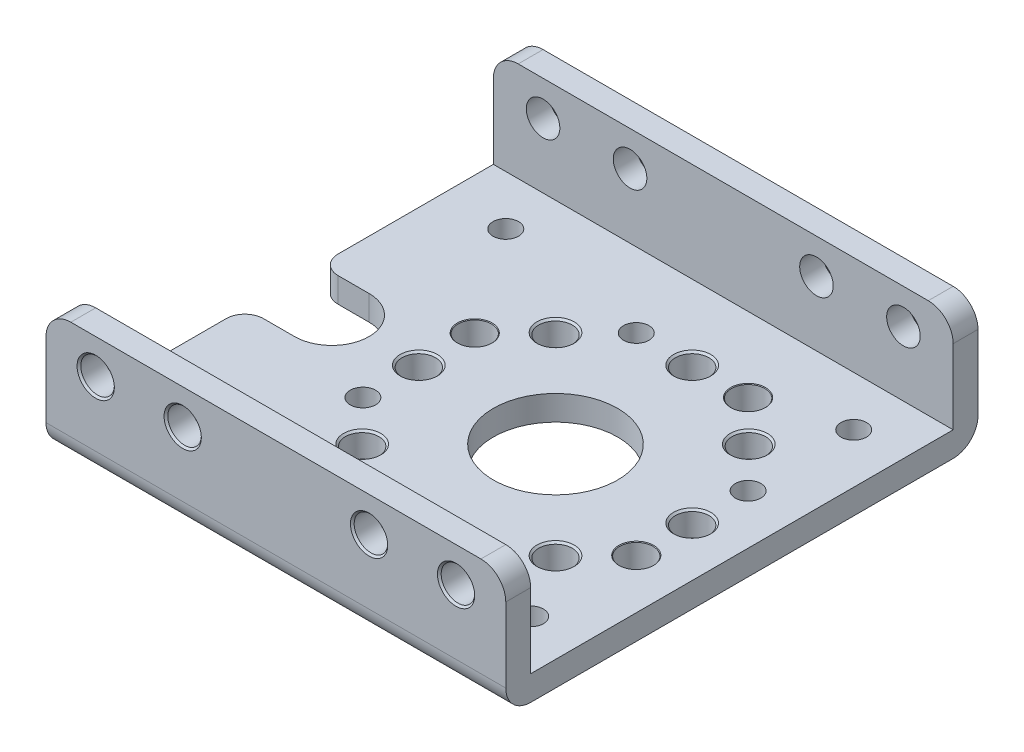
SolidWorks part; units mm, degrees
ref_plane "Front Plane" through (0, 0, 0) normal (0, 0, 1) x (1, 0, 0)
ref_plane "Top Plane" through (0, 0, 0) normal (0, 1, 0) x (1, 0, 0)
ref_plane "Right Plane" through (0, 0, 0) normal (1, 0, 0) x (0, 0, -1)
ref_plane "Plane1" through (0, 10, 0) normal (0, 1, 0) x (-1, 0, 0)
sketch "Sketch1" plane through (0, 10, 0) normal (0, 1, 0) x (-1, 0, 0)
  line L0 (22, 19) -> (-15, 19)
  line L1 (-15, 19) -> (-15, -19)
  line L2 (-15, -19) -> (22, -19)
  line L3 (22, -19) -> (22, 19)
extrude "Boss-Extrude1" add sketch "Sketch1" against normal blind 10
sketch "Sketch2" plane through (15, 0, 0) normal (1, 0, 0) x (0, 0, -1)
  line L0 (17, 10) -> (-17, 10)
  line L1 (-17, 10) -> (-17, 2)
  line L2 (-17, 2) -> (17, 2)
  line L3 (17, 2) -> (17, 10)
extrude "Cut-Extrude1" cut sketch "Sketch2" against normal through all
sketch "Sketch3" plane through (0, 2, 0) normal (0, 1, 0) x (-1, 0, 0)
  line L0 (22, -3) -> (22, 3)
  line L1 (22, 3) -> (18, 3)
  line L2 (18, -3) -> (22, -3)
  arc A0 (18, 3) -> (18, -3) centre (18, 0) ccw
extrude "Cut-Extrude2" cut sketch "Sketch3" against normal through all
hole_wizard "Hole1" positions "Sketch5" profile "Sketch4" legacy
sketch "Sketch5" plane through (0, 0, 0) normal (0, -1, 0) x (1, 0, 0)
  point P0 (-4.5, -11)
sketch "Sketch4" plane through (-4.5, 0, -11) normal (1, 0, 0) x (0, 0, -1)
  line L0 (0, 0) -> (0, 10)
  line L1 (0, 10) -> (1.025, 10)
  line L2 (1.025, 10) -> (1.025, 0)
  line L3 (1.025, 0) -> (0, 0)
  line L4 (0, 110) -> (0, -10) construction
  dimension "Diameter" = 2.05
  dimension "Depth" = 10
hole_wizard "Hole2" positions "Sketch7" profile "Sketch6" legacy
sketch "Sketch7" plane through (0, 0, 0) normal (0, -1, 0) x (1, 0, 0)
  point P0 (-11, 4.5)
sketch "Sketch6" plane through (-11, 0, 4.5) normal (1, 0, 0) x (0, 0, -1)
  line L0 (0, 0) -> (0, 10)
  line L1 (0, 10) -> (1.025, 10)
  line L2 (1.025, 10) -> (1.025, 0)
  line L3 (1.025, 0) -> (0, 0)
  line L4 (0, 110) -> (0, -10) construction
  dimension "Diameter" = 2.05
  dimension "Depth" = 10
hole_wizard "Hole3" positions "Sketch9" profile "Sketch8" legacy
sketch "Sketch9" plane through (0, 0, 0) normal (0, -1, 0) x (1, 0, 0)
  point P0 (4.5, 11)
sketch "Sketch8" plane through (4.5, 0, 11) normal (1, 0, 0) x (0, 0, -1)
  line L0 (0, 0) -> (0, 10)
  line L1 (0, 10) -> (1.025, 10)
  line L2 (1.025, 10) -> (1.025, 0)
  line L3 (1.025, 0) -> (0, 0)
  line L4 (0, 110) -> (0, -10) construction
  dimension "Diameter" = 2.05
  dimension "Depth" = 10
hole_wizard "Hole4" positions "Sketch11" profile "Sketch10" legacy
sketch "Sketch11" plane through (0, 0, 0) normal (0, -1, 0) x (1, 0, 0)
  point P0 (11, -4.5)
sketch "Sketch10" plane through (11, 0, -4.5) normal (1, 0, 0) x (0, 0, -1)
  line L0 (0, 0) -> (0, 10)
  line L1 (0, 10) -> (1.025, 10)
  line L2 (1.025, 10) -> (1.025, 0)
  line L3 (1.025, 0) -> (0, 0)
  line L4 (0, 110) -> (0, -10) construction
  dimension "Diameter" = 2.05
  dimension "Depth" = 10
hole_wizard "Hole5" positions "Sketch13" profile "Sketch12" legacy
sketch "Sketch13" plane through (0, 0, 0) normal (0, -1, 0) x (1, 0, 0)
  point P0 (-17, 13)
sketch "Sketch12" plane through (-17, 0, 13) normal (1, 0, 0) x (0, 0, -1)
  line L0 (0, 0) -> (0, 10)
  line L1 (0, 10) -> (1.025, 10)
  line L2 (1.025, 10) -> (1.025, 0)
  line L3 (1.025, 0) -> (0, 0)
  line L4 (0, 110) -> (0, -10) construction
  dimension "Diameter" = 2.05
  dimension "Depth" = 10
hole_wizard "Hole6" positions "Sketch15" profile "Sketch14" legacy
sketch "Sketch15" plane through (0, 0, 0) normal (0, -1, 0) x (1, 0, 0)
  point P0 (-17, -13)
sketch "Sketch14" plane through (-17, 0, -13) normal (1, 0, 0) x (0, 0, -1)
  line L0 (0, 0) -> (0, 10)
  line L1 (0, 10) -> (1.025, 10)
  line L2 (1.025, 10) -> (1.025, 0)
  line L3 (1.025, 0) -> (0, 0)
  line L4 (0, 110) -> (0, -10) construction
  dimension "Diameter" = 2.05
  dimension "Depth" = 10
hole_wizard "Hole7" positions "Sketch17" profile "Sketch16" legacy
sketch "Sketch17" plane through (0, 0, 0) normal (0, -1, 0) x (1, 0, 0)
  point P0 (11, 13)
sketch "Sketch16" plane through (11, 0, 13) normal (1, 0, 0) x (0, 0, -1)
  line L0 (0, 0) -> (0, 10)
  line L1 (0, 10) -> (1.025, 10)
  line L2 (1.025, 10) -> (1.025, 0)
  line L3 (1.025, 0) -> (0, 0)
  line L4 (0, 110) -> (0, -10) construction
  dimension "Diameter" = 2.05
  dimension "Depth" = 10
hole_wizard "Hole8" positions "Sketch19" profile "Sketch18" legacy
sketch "Sketch19" plane through (0, 0, 0) normal (0, -1, 0) x (1, 0, 0)
  point P0 (11, -13)
sketch "Sketch18" plane through (11, 0, -13) normal (1, 0, 0) x (0, 0, -1)
  line L0 (0, 0) -> (0, 10)
  line L1 (0, 10) -> (1.025, 10)
  line L2 (1.025, 10) -> (1.025, 0)
  line L3 (1.025, 0) -> (0, 0)
  line L4 (0, 110) -> (0, -10) construction
  dimension "Diameter" = 2.05
  dimension "Depth" = 10
hole_wizard "Hole9" positions "Sketch21" profile "Sketch20" legacy
sketch "Sketch21" plane through (0, 0, 0) normal (0, -1, 0) x (1, 0, 0)
  point P0 (0, 0)
sketch "Sketch20" plane through (0, 0, 0) normal (1, 0, 0) x (0, 0, -1)
  line L0 (0, 0) -> (0, 10)
  line L1 (0, 10) -> (5, 10)
  line L2 (5, 10) -> (5, 0)
  line L3 (5, 0) -> (0, 0)
  line L4 (0, 110) -> (0, -10) construction
  dimension "Diameter" = 10
  dimension "Depth" = 10
hole_wizard "Hole10" positions "Sketch23" profile "Sketch22" legacy
sketch "Sketch23" plane through (0, 2, 0) normal (0, 1, 0) x (-1, 0, 0)
  point P0 (11, -4.5)
sketch "Sketch22" plane through (-11, 2, -4.5) normal (1, 0, 0) x (0, 0, 1)
  line L0 (0, 0) -> (0, 2)
  line L1 (0, 2) -> (1.35, 2)
  line L2 (1.35, 2) -> (1.35, 0)
  line L3 (1.35, 0) -> (0, 0)
  line L4 (0, 110) -> (0, -10) construction
  dimension "Diameter" = 2.7
  dimension "Depth" = 2
hole_wizard "Hole11" positions "Sketch25" profile "Sketch24" legacy
sketch "Sketch25" plane through (0, 2, 0) normal (0, 1, 0) x (-1, 0, 0)
  point P0 (4.5, 11)
sketch "Sketch24" plane through (-4.5, 2, 11) normal (1, 0, 0) x (0, 0, 1)
  line L0 (0, 0) -> (0, 2)
  line L1 (0, 2) -> (1.35, 2)
  line L2 (1.35, 2) -> (1.35, 0)
  line L3 (1.35, 0) -> (0, 0)
  line L4 (0, 110) -> (0, -10) construction
  dimension "Diameter" = 2.7
  dimension "Depth" = 2
hole_wizard "Hole12" positions "Sketch27" profile "Sketch26" legacy
sketch "Sketch27" plane through (0, 2, 0) normal (0, 1, 0) x (-1, 0, 0)
  point P0 (-11, 4.5)
sketch "Sketch26" plane through (11, 2, 4.5) normal (1, 0, 0) x (0, 0, 1)
  line L0 (0, 0) -> (0, 2)
  line L1 (0, 2) -> (1.35, 2)
  line L2 (1.35, 2) -> (1.35, 0)
  line L3 (1.35, 0) -> (0, 0)
  line L4 (0, 110) -> (0, -10) construction
  dimension "Diameter" = 2.7
  dimension "Depth" = 2
hole_wizard "Hole13" positions "Sketch29" profile "Sketch28" legacy
sketch "Sketch29" plane through (0, 2, 0) normal (0, 1, 0) x (-1, 0, 0)
  point P0 (-4.5, -11)
sketch "Sketch28" plane through (4.5, 2, -11) normal (1, 0, 0) x (0, 0, 1)
  line L0 (0, 0) -> (0, 2)
  line L1 (0, 2) -> (1.35, 2)
  line L2 (1.35, 2) -> (1.35, 0)
  line L3 (1.35, 0) -> (0, 0)
  line L4 (0, 110) -> (0, -10) construction
  dimension "Diameter" = 2.7
  dimension "Depth" = 2
hole_wizard "Hole14" positions "Sketch31" profile "Sketch30" legacy
sketch "Sketch31" plane through (0, 2, 0) normal (0, 1, 0) x (-1, 0, 0)
  point P0 (-7.7782, 7.7782)
sketch "Sketch30" plane through (7.7782, 2, 7.7782) normal (1, 0, 0) x (0, 0, 1)
  line L0 (0, 0) -> (0, 2)
  line L1 (0, 2) -> (1.35, 2)
  line L2 (1.35, 2) -> (1.35, 0)
  line L3 (1.35, 0) -> (0, 0)
  line L4 (0, 110) -> (0, -10) construction
  dimension "Diameter" = 2.7
  dimension "Depth" = 2
hole_wizard "Hole15" positions "Sketch33" profile "Sketch32" legacy
sketch "Sketch33" plane through (0, 2, 0) normal (0, 1, 0) x (-1, 0, 0)
  point P0 (0, 11)
sketch "Sketch32" plane through (0, 2, 11) normal (1, 0, 0) x (0, 0, 1)
  line L0 (0, 0) -> (0, 2)
  line L1 (0, 2) -> (1.35, 2)
  line L2 (1.35, 2) -> (1.35, 0)
  line L3 (1.35, 0) -> (0, 0)
  line L4 (0, 110) -> (0, -10) construction
  dimension "Diameter" = 2.7
  dimension "Depth" = 2
hole_wizard "Hole16" positions "Sketch35" profile "Sketch34" legacy
sketch "Sketch35" plane through (0, 2, 0) normal (0, 1, 0) x (-1, 0, 0)
  point P0 (7.7782, 7.7782)
sketch "Sketch34" plane through (-7.7782, 2, 7.7782) normal (1, 0, 0) x (0, 0, 1)
  line L0 (0, 0) -> (0, 2)
  line L1 (0, 2) -> (1.35, 2)
  line L2 (1.35, 2) -> (1.35, 0)
  line L3 (1.35, 0) -> (0, 0)
  line L4 (0, 110) -> (0, -10) construction
  dimension "Diameter" = 2.7
  dimension "Depth" = 2
hole_wizard "Hole17" positions "Sketch37" profile "Sketch36" legacy
sketch "Sketch37" plane through (0, 2, 0) normal (0, 1, 0) x (-1, 0, 0)
  point P0 (11, 0)
sketch "Sketch36" plane through (-11, 2, 0) normal (1, 0, 0) x (0, 0, 1)
  line L0 (0, 0) -> (0, 2)
  line L1 (0, 2) -> (1.35, 2)
  line L2 (1.35, 2) -> (1.35, 0)
  line L3 (1.35, 0) -> (0, 0)
  line L4 (0, 110) -> (0, -10) construction
  dimension "Diameter" = 2.7
  dimension "Depth" = 2
hole_wizard "Hole18" positions "Sketch39" profile "Sketch38" legacy
sketch "Sketch39" plane through (0, 2, 0) normal (0, 1, 0) x (-1, 0, 0)
  point P0 (7.7782, -7.7782)
sketch "Sketch38" plane through (-7.7782, 2, -7.7782) normal (1, 0, 0) x (0, 0, 1)
  line L0 (0, 0) -> (0, 2)
  line L1 (0, 2) -> (1.35, 2)
  line L2 (1.35, 2) -> (1.35, 0)
  line L3 (1.35, 0) -> (0, 0)
  line L4 (0, 110) -> (0, -10) construction
  dimension "Diameter" = 2.7
  dimension "Depth" = 2
hole_wizard "Hole19" positions "Sketch41" profile "Sketch40" legacy
sketch "Sketch41" plane through (0, 2, 0) normal (0, 1, 0) x (-1, 0, 0)
  point P0 (0, -11)
sketch "Sketch40" plane through (0, 2, -11) normal (1, 0, 0) x (0, 0, 1)
  line L0 (0, 0) -> (0, 2)
  line L1 (0, 2) -> (1.35, 2)
  line L2 (1.35, 2) -> (1.35, 0)
  line L3 (1.35, 0) -> (0, 0)
  line L4 (0, 110) -> (0, -10) construction
  dimension "Diameter" = 2.7
  dimension "Depth" = 2
hole_wizard "Hole20" positions "Sketch43" profile "Sketch42" legacy
sketch "Sketch43" plane through (0, 2, 0) normal (0, 1, 0) x (-1, 0, 0)
  point P0 (-7.7782, -7.7782)
sketch "Sketch42" plane through (7.7782, 2, -7.7782) normal (1, 0, 0) x (0, 0, 1)
  line L0 (0, 0) -> (0, 2)
  line L1 (0, 2) -> (1.35, 2)
  line L2 (1.35, 2) -> (1.35, 0)
  line L3 (1.35, 0) -> (0, 0)
  line L4 (0, 110) -> (0, -10) construction
  dimension "Diameter" = 2.7
  dimension "Depth" = 2
hole_wizard "Hole21" positions "Sketch45" profile "Sketch44" legacy
sketch "Sketch45" plane through (0, 2, 0) normal (0, 1, 0) x (-1, 0, 0)
  point P0 (-11, 0)
sketch "Sketch44" plane through (11, 2, 0) normal (1, 0, 0) x (0, 0, 1)
  line L0 (0, 0) -> (0, 2)
  line L1 (0, 2) -> (1.35, 2)
  line L2 (1.35, 2) -> (1.35, 0)
  line L3 (1.35, 0) -> (0, 0)
  line L4 (0, 110) -> (0, -10) construction
  dimension "Diameter" = 2.7
  dimension "Depth" = 2
hole_wizard "Hole22" positions "Sketch47" profile "Sketch46" legacy
sketch "Sketch47" plane through (0, 0, 19) normal (0, 0, 1) x (1, 0, 0)
  point P0 (-11, 7.2)
sketch "Sketch46" plane through (-11, 7.2, 19) normal (1, 0, 0) x (0, -1, 0)
  line L0 (0, 0) -> (0, 2)
  line L1 (0, 2) -> (1.35, 2)
  line L2 (1.35, 2) -> (1.35, 0)
  line L3 (1.35, 0) -> (0, 0)
  line L4 (0, 110) -> (0, -10) construction
  dimension "Diameter" = 2.7
  dimension "Depth" = 2
hole_wizard "Hole23" positions "Sketch49" profile "Sketch48" legacy
sketch "Sketch49" plane through (0, 0, 19) normal (0, 0, 1) x (1, 0, 0)
  point P0 (11, 7.2)
sketch "Sketch48" plane through (11, 7.2, 19) normal (1, 0, 0) x (0, -1, 0)
  line L0 (0, 0) -> (0, 2)
  line L1 (0, 2) -> (1.35, 2)
  line L2 (1.35, 2) -> (1.35, 0)
  line L3 (1.35, 0) -> (0, 0)
  line L4 (0, 110) -> (0, -10) construction
  dimension "Diameter" = 2.7
  dimension "Depth" = 2
hole_wizard "Hole24" positions "Sketch51" profile "Sketch50" legacy
sketch "Sketch51" plane through (0, 0, 19) normal (0, 0, 1) x (1, 0, 0)
  point P0 (-18, 7.2)
sketch "Sketch50" plane through (-18, 7.2, 19) normal (1, 0, 0) x (0, -1, 0)
  line L0 (0, 0) -> (0, 2)
  line L1 (0, 2) -> (1.35, 2)
  line L2 (1.35, 2) -> (1.35, 0)
  line L3 (1.35, 0) -> (0, 0)
  line L4 (0, 110) -> (0, -10) construction
  dimension "Diameter" = 2.7
  dimension "Depth" = 2
hole_wizard "Hole25" positions "Sketch53" profile "Sketch52" legacy
sketch "Sketch53" plane through (0, 0, 19) normal (0, 0, 1) x (1, 0, 0)
  point P0 (4, 7.2)
sketch "Sketch52" plane through (4, 7.2, 19) normal (1, 0, 0) x (0, -1, 0)
  line L0 (0, 0) -> (0, 2)
  line L1 (0, 2) -> (1.35, 2)
  line L2 (1.35, 2) -> (1.35, 0)
  line L3 (1.35, 0) -> (0, 0)
  line L4 (0, 110) -> (0, -10) construction
  dimension "Diameter" = 2.7
  dimension "Depth" = 2
hole_wizard "Hole26" positions "Sketch55" profile "Sketch54" legacy
sketch "Sketch55" plane through (0, 0, -19) normal (0, 0, -1) x (-1, 0, 0)
  point P0 (11, 7.2)
sketch "Sketch54" plane through (-11, 7.2, -19) normal (1, 0, 0) x (0, 1, 0)
  line L0 (0, 0) -> (0, 38)
  line L1 (0, 38) -> (1.35, 38)
  line L2 (1.35, 38) -> (1.35, 0)
  line L3 (1.35, 0) -> (0, 0)
  line L4 (0, 110) -> (0, -10) construction
  dimension "Diameter" = 2.7
  dimension "Depth" = 38
hole_wizard "Hole27" positions "Sketch57" profile "Sketch56" legacy
sketch "Sketch57" plane through (0, 0, -19) normal (0, 0, -1) x (-1, 0, 0)
  point P0 (-11, 7.2)
sketch "Sketch56" plane through (11, 7.2, -19) normal (1, 0, 0) x (0, 1, 0)
  line L0 (0, 0) -> (0, 38)
  line L1 (0, 38) -> (1.35, 38)
  line L2 (1.35, 38) -> (1.35, 0)
  line L3 (1.35, 0) -> (0, 0)
  line L4 (0, 110) -> (0, -10) construction
  dimension "Diameter" = 2.7
  dimension "Depth" = 38
hole_wizard "Hole28" positions "Sketch59" profile "Sketch58" legacy
sketch "Sketch59" plane through (0, 0, -19) normal (0, 0, -1) x (-1, 0, 0)
  point P0 (18, 7.2)
sketch "Sketch58" plane through (-18, 7.2, -19) normal (1, 0, 0) x (0, 1, 0)
  line L0 (0, 0) -> (0, 38)
  line L1 (0, 38) -> (1.35, 38)
  line L2 (1.35, 38) -> (1.35, 0)
  line L3 (1.35, 0) -> (0, 0)
  line L4 (0, 110) -> (0, -10) construction
  dimension "Diameter" = 2.7
  dimension "Depth" = 38
hole_wizard "Hole29" positions "Sketch61" profile "Sketch60" legacy
sketch "Sketch61" plane through (0, 0, -19) normal (0, 0, -1) x (-1, 0, 0)
  point P0 (-4, 7.2)
sketch "Sketch60" plane through (4, 7.2, -19) normal (1, 0, 0) x (0, 1, 0)
  line L0 (0, 0) -> (0, 38)
  line L1 (0, 38) -> (1.35, 38)
  line L2 (1.35, 38) -> (1.35, 0)
  line L3 (1.35, 0) -> (0, 0)
  line L4 (0, 110) -> (0, -10) construction
  dimension "Diameter" = 2.7
  dimension "Depth" = 38
chamfer "Chamfer1" distance 0.15 angle 45 1 edges at (7.7782, 2, -6.4282)
chamfer "Chamfer2" distance 0.15 angle 45 1 edges at (2.65, 7.2, -19)
chamfer "Chamfer3" distance 0.15 angle 45 1 edges at (11, 2, 1.35)
chamfer "Chamfer4" distance 0.15 angle 45 1 edges at (-11, 2, 1.35)
chamfer "Chamfer5" distance 0.15 angle 45 1 edges at (-7.7782, 2, -6.4282)
chamfer "Chamfer6" distance 0.15 angle 45 1 edges at (-9.65, 7.2, 19)
chamfer "Chamfer7" distance 0.15 angle 45 1 edges at (0, 2, -9.65)
chamfer "Chamfer8" distance 0.15 angle 45 1 edges at (-16.65, 7.2, 19)
chamfer "Chamfer9" distance 0.15 angle 45 1 edges at (9.65, 7.2, -19)
chamfer "Chamfer10" distance 0.15 angle 45 1 edges at (-12.35, 7.2, -19)
chamfer "Chamfer11" distance 0.15 angle 45 1 edges at (-19.35, 7.2, -19)
chamfer "Chamfer12" distance 0.05 angle 45 1 edges at (-4.5, 2, 12.35)
chamfer "Chamfer13" distance 0.375 angle 45 1 edges at (-4.5, 0, -12.025)
chamfer "Chamfer14" distance 0.05 angle 45 1 edges at (4.5, 2, -9.65)
chamfer "Chamfer15" distance 0.375 angle 45 1 edges at (-11, 0, 3.475)
chamfer "Chamfer16" distance 0.15 angle 45 1 edges at (0, 2, 12.35)
chamfer "Chamfer17" distance 0.375 angle 45 1 edges at (4.5, 0, 9.975)
chamfer "Chamfer18" distance 0.325 angle 45 1 edges at (11, 0, -14.025)
chamfer "Chamfer19" distance 0.375 angle 45 1 edges at (11, 0, -5.525)
chamfer "Chamfer20" distance 0.15 angle 45 1 edges at (5.35, 7.2, 19)
chamfer "Chamfer21" distance 0.325 angle 45 1 edges at (-17, 0, 11.975)
chamfer "Chamfer22" distance 0.05 angle 45 1 edges at (11, 2, 5.85)
chamfer "Chamfer23" distance 0.325 angle 45 1 edges at (-17, 0, -14.025)
chamfer "Chamfer24" distance 0.15 angle 45 1 edges at (-7.7782, 2, 9.1282)
chamfer "Chamfer25" distance 0.325 angle 45 1 edges at (11, 0, 11.975)
chamfer "Chamfer26" distance 0.05 angle 45 1 edges at (-11, 2, -3.15)
chamfer "Chamfer27" distance 0.15 angle 45 1 edges at (12.35, 7.2, 19)
chamfer "Chamfer28" distance 0.15 angle 45 1 edges at (7.7782, 2, 9.1282)
fillet "Fillet1" radius 1.5 1 edges at (-22, 1, -3)
fillet "Fillet2" radius 1.5 1 edges at (-22, 1, 3)
fillet "Fillet3" radius 2 1 edges at (-3.5, 0, -19)
fillet "Fillet4" radius 2 1 edges at (15, 10, 18)
fillet "Fillet5" radius 2 1 edges at (-22, 10, 18)
fillet "Fillet6" radius 2 1 edges at (-22, 10, -18)
fillet "Fillet7" radius 2 1 edges at (15, 10, -18)
fillet "Fillet8" radius 2 1 edges at (-3.5, 0, 19)
